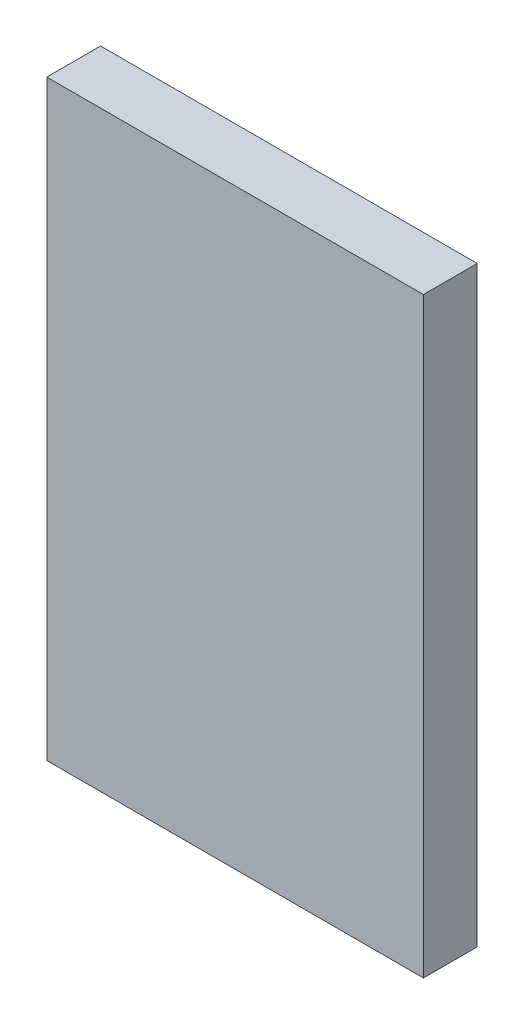
SolidWorks part; units mm, degrees
material "Oak"
ref_plane "Front Plane" through (0, 0, 0) normal (0, 0, 1) x (1, 0, 0)
ref_plane "Top Plane" through (0, 0, 0) normal (0, 1, 0) x (1, 0, 0)
ref_plane "Right Plane" through (0, 0, 0) normal (1, 0, 0) x (0, 0, -1)
sketch "Sketch1" plane through (0, 0, 0) normal (0, 0, 1) x (1, 0, 0)
  line L1 (-88.9, -139.7) -> (88.9, -139.7)
  line L2 (-88.9, -139.7) -> (-88.9, 139.7)
  line L3 (-88.9, 139.7) -> (88.9, 139.7)
  line L4 (88.9, -139.7) -> (88.9, 139.7)
  line L5 (-88.9, -139.7) -> (88.9, 139.7) construction
  line L6 (-88.9, 139.7) -> (88.9, -139.7) construction
  point P0 (0, 0)
  dimension "D1" = 279.4
  dimension "D2" = 177.8
extrude "Boss-Extrude1" add sketch "Sketch1" along normal blind 25.4
